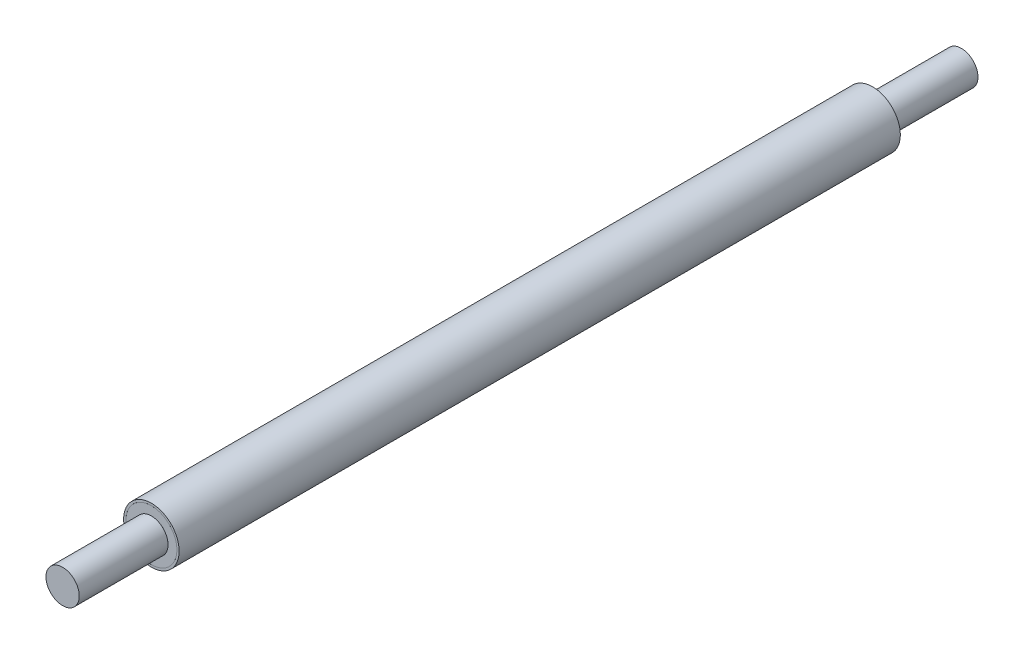
SolidWorks part; units mm, degrees
ref_plane "Front Plane" through (0, 0, 0) normal (0, 0, 1) x (1, 0, 0)
ref_plane "Top Plane" through (0, 0, 0) normal (0, 1, 0) x (1, 0, 0)
ref_plane "Right Plane" through (0, 0, 0) normal (1, 0, 0) x (0, 0, -1)
sketch "Sketch1" plane through (0, 0, 0) normal (0, 0, 1) x (1, 0, 0)
  circle A0 centre (0, 0) radius 25
  dimension "D1" = 50
extrude "Boss-Extrude1" add sketch "Sketch1" along normal mid plane 650
sketch "Sketch2" plane through (0, 0, 325) normal (0, 0, 1) x (1, 0, 0)
  circle A0 centre (0, 0) radius 15
  dimension "D1" = 30
extrude "Boss-Extrude2" add sketch "Sketch2" along normal blind 80 separate body
mirror "Mirror1" about plane through (0, 0, 0) normal (0, 0, 1) of bodies 102
shell "Shell1" thickness 2
sketch "Sketch3" plane through (0, 0, -325) normal (0, 0, -1) x (-1, 0, 0)
  circle A0 centre (0, 0) radius 23 construction
  circle A1 centre (0, 0) radius 15 construction
  circle A2 centre (0, 0) radius 23
  circle A3 centre (0, 0) radius 15
extrude "Boss-Extrude3" add sketch "Sketch3" against normal blind 10 separate body
mirror "Mirror2" about plane through (0, 0, 0) normal (0, 0, 1) of bodies 104
